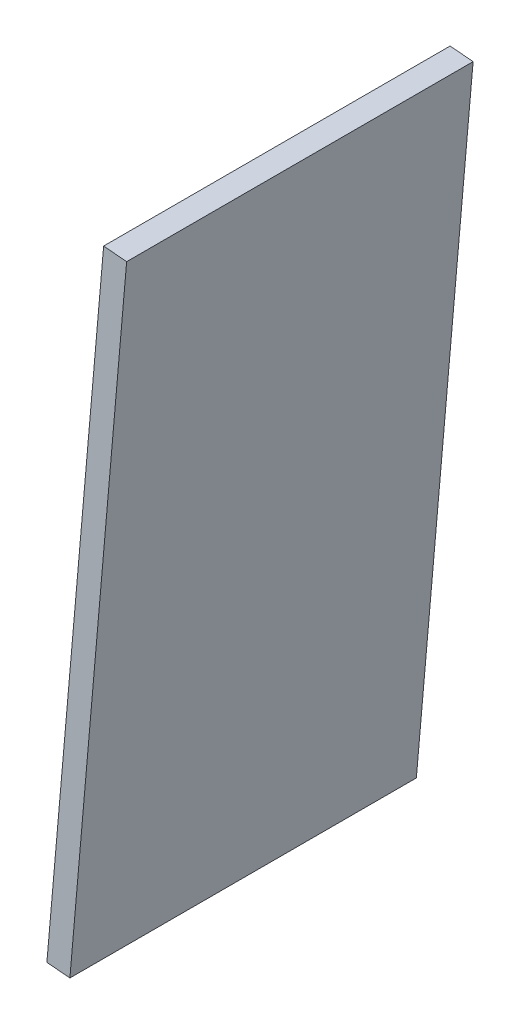
SolidWorks part; units mm, degrees
ref_plane "Front Plane" through (0, 0, 0) normal (0, 0, 1) x (1, 0, 0)
ref_plane "Top Plane" through (0, 0, 0) normal (0, 1, 0) x (1, 0, 0)
ref_plane "Right Plane" through (0, 0, 0) normal (1, 0, 0) x (0, 0, -1)
sketch "Sketch1" plane through (0, 0, 0) normal (0, 0, 1) x (1, 0, 0)
  line L0 (0, 0) -> (36.6665, 419.1) construction
  line L1 (36.6665, 419.1) -> (155.7226, 419.1) construction
  line L2 (155.7226, 419.1) -> (155.7226, 0) construction
  line L3 (155.7226, 0) -> (0, 0) construction
  line L4 (155.7226, -1000) -> (155.7226, 49000) construction
  line L5 (1.8042, 20.6221) -> (36.6665, 419.1) construction
  line L6 (1.8042, 20.6221) -> (41.652, 17.1359) construction
  line L7 (36.6665, 419.1) -> (76.5143, 415.6138) construction
  line L8 (41.652, 17.1359) -> (76.5143, 415.6138) construction
  line L9 (60.4726, -1000) -> (60.4726, 49000) construction
  line L10 (-52.7184, 317.5) -> (-128.6284, 324.1413) construction
  line L11 (-30.1965, 414.3375) -> (36.6601, 414.3375) construction
  line L12 (-1162.1335, 304.8) -> (48837.8665, 304.8) construction
  line L13 (-130.0274, 292.1) -> (-53.8274, 292.1) construction
  line L14 (-128.6284, 324.1413) -> (-53.8274, 292.1) construction
  line L15 (-52.7184, 317.5) -> (-130.0274, 292.1) construction
  line L16 (36.6601, 338.1375) -> (-30.1965, 338.1375) construction
  line L17 (-138.1172, 324.9714) -> (27.1662, 310.511)
  line L18 (-138.1172, 324.9714) -> (-137.5638, 331.2973)
  line L19 (-137.5638, 331.2973) -> (36.6665, 419.1)
  line L20 (36.6665, 419.1) -> (104.9226, 419.1)
  line L21 (104.9226, 419.1) -> (104.9226, 0) construction
  line L22 (27.1662, 310.511) -> (0.3389, 3.8741)
  line L23 (0.3389, 3.8741) -> (44.6198, 0)
  line L24 (44.6198, 0) -> (104.9226, 0)
  line L25 (104.9226, 419.1) -> (155.7226, 311.15)
  line L26 (155.7226, 311.15) -> (155.7226, 304.8)
  line L27 (155.7226, 304.8) -> (104.9226, 280.8941)
  line L28 (104.9226, 280.8941) -> (104.9226, 0)
  arc A0 (-128.6284, 324.1413) -> (-30.1965, 414.3375) centre (-30.1965, 315.5296) cw construction
  arc A1 (69.9976, 304.8) -> (36.6601, 338.1375) centre (36.6601, 304.8) ccw construction
  arc A2 (146.1976, 304.8) -> (36.6601, 414.3375) centre (36.6601, 304.8) ccw construction
  arc A3 (-52.7184, 317.5) -> (-30.1965, 338.1375) centre (-30.1965, 315.5296) cw construction
  point P7 (54.1226, 400.05)
  point P17 (146.1976, 304.8)
  point P18 (69.9976, 304.8)
  dimension "D9" = 9.525
  dimension "D14" = 25.4
  dimension "D1" = 419.1
  dimension "D2" = 101.6
  dimension "D3" = 19.05
  dimension "D4" = 19.05
  dimension "D5" = 85
  dimension "D6" = 40
  dimension "D7" = 400
  dimension "D8" = 95.25
  dimension "D10" = 9.525
  dimension "D11" = 114.3
  dimension "D12" = 76.2
  dimension "D13" = 9.525
  dimension "D15" = 127
  dimension "D16" = 9.525
  dimension "D17" = 209.55
  dimension "D18" = 6.35
  dimension "D19" = 50.8
  dimension "D20" = 44.45
  dimension "D21" = 6.35
sketch "Sketch2" plane through (0, 0, 0) normal (0, 0, 1) x (1, 0, 0)
  line L0 (38.543, 0.5317) -> (44.8688, -0.0218)
  line L1 (38.543, 0.5317) -> (54.1468, 178.8835)
  line L2 (44.8688, -0.0218) -> (60.4726, 178.3301)
  line L3 (54.1468, 178.8835) -> (60.4726, 178.3301)
  line L6 (0.3389, 3.8741) -> (44.6198, 0) construction
  line L7 (27.1662, 310.511) -> (0.3389, 3.8741) construction
  line L8 (60.4726, -201000) -> (60.4726, 249000) construction
  dimension "D1" = 6.35
  dimension "D2" = 38.35
extrude "Boss-Extrude1" add sketch "Sketch2" along normal blind 95.25
